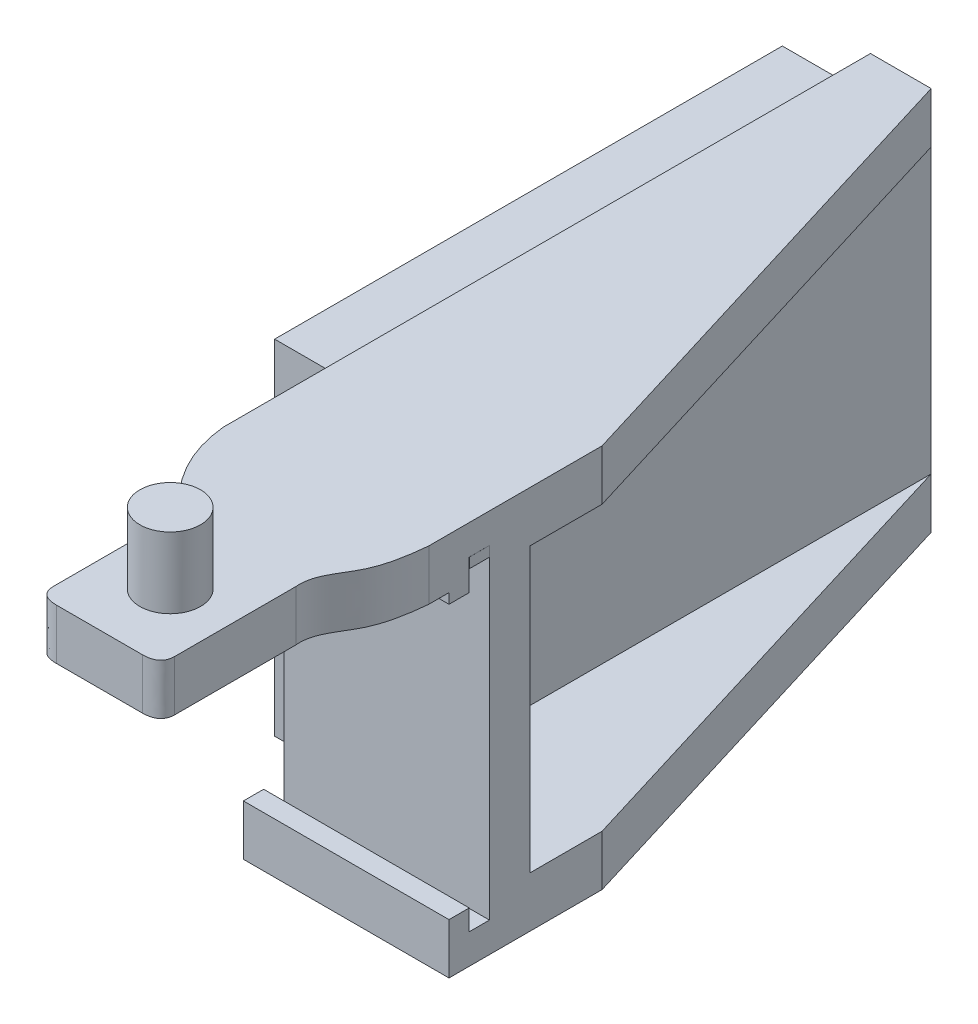
SolidWorks part; units mm, degrees
ref_plane "Alzado" through (0, 0, 0) normal (0, 0, 1) x (1, 0, 0)
ref_plane "Planta" through (0, 0, 0) normal (0, 1, 0) x (1, 0, 0)
ref_plane "Vista lateral" through (0, 0, 0) normal (1, 0, 0) x (0, 0, -1)
sketch "Croquis1" plane through (0, 0, 0) normal (0, 1, 0) x (1, 0, 0)
  line L0 (0, 30) -> (0, 0)
  line L1 (0, 0) -> (0, -2)
  line L2 (2.6172, -13.0183) -> (2.6172, -7.3446)
  line L4 (8.6172, -13.0183) -> (8.6172, -7.0183)
  line L5 (10.1631, 6.5705) -> (10.1631, 0)
  line L6 (10.1631, -2) -> (10.1631, 0)
  line L7 (10.1631, 6.5705) -> (3, 30)
  line L8 (3, 30) -> (0, 30)
  line L9 (3.4899, -13.7374) -> (7.7445, -13.7374)
  spline S0 degree 3 poles (8.6172, -7.0183) (8.5294, -6.0662) (9.8153, -4.7072) (10.0769, -2.8869) (10.1631, -2) knots 0 0 0 0 0.490317 1 1 1 1
  spline S1 degree 2 poles (0, -2) (0.2441, -4.453) (2.0609, -6.2319) knots 0 0 0 1 1 1
  spline S2 degree 2 poles (2.0609, -6.2319) (2.507, -6.7126) (2.6172, -7.3446) knots 0 0 0 1 1 1
  spline S3 degree 2 poles (2.6172, -13.0183) (2.6309, -13.735) (3.4899, -13.7374) knots 0 0 0 1 1 1
  spline S4 degree 2 poles (8.6172, -13.0183) (8.6035, -13.735) (7.7445, -13.7374) knots 0 0 0 1 1 1
  dimension "D1" = 3
  dimension "D2" = 30
  dimension "D3" = 24.5
  dimension "D4" = 6
  dimension "D6" = 2
  dimension "D7" = 6
extrude "Saliente-Extruir1" add sketch "Croquis1" along normal blind 19
sketch "Croquis2" plane through (0, 0, -30) normal (0, 0, -1) x (-1, 0, 0)
  line L0 (-3, 19) -> (-3, 16.5)
  line L1 (-3, 19) -> (-3, 0) construction
  line L2 (-3, 16.5) -> (-12.8726, 16.5)
  line L3 (-12.8726, 16.5) -> (-12.8726, 2.5)
  line L4 (-12.8726, 2.5) -> (-3, 2.5)
  line L5 (-3, 2.5) -> (-3, 16.5)
  line M6 (-3, 19) -> (-3, 0)
  dimension "D1" = 2.5
  dimension "D2" = 2.5
extrude "Cortar-Extruir1" cut sketch "Croquis2" against normal blind 27 contours L3 L4 L2 M6
sketch "Croquis10" plane through (0, 0, 0) normal (1, 0, 0) x (0, 0, -1)
  line L0 (1, 2.5) -> (1, 16.5)
  line L1 (1, 2.5) -> (-1, 2.5)
  line L2 (1, 16.5) -> (-13.7374, 16.5)
  line L3 (-13.7374, 19) -> (-13.7374, 0) construction
  line L4 (-13.7374, 16.5) -> (-13.7374, 0)
  line L5 (-1, 2.5) -> (-1, 0)
  line L7 (-2, 0) -> (6.5705, 0) construction
  line L8 (-1, 0) -> (-13.7374, 0)
  dimension "D1" = 2
extrude "Cortar-Extruir2" cut sketch "Croquis10" along normal through all both and the other way through all
sketch "Croquis11" plane through (0, 0, 0) normal (1, 0, 0) x (0, 0, -1)
  line L0 (1, 2.5) -> (1, 1.4799)
  line L1 (1, 1.4799) -> (0, 1.4799)
  line L2 (0, 1.4799) -> (0, 2.5)
  line L3 (-1, 2.5) -> (1, 2.5) construction
  line L4 (0, 2.5) -> (1, 2.5)
  line L5 (1, 16.5) -> (1, 17.5201)
  line L8 (1, 17.5201) -> (0, 17.5201)
  line L9 (0, 17.5201) -> (0, 16.5)
  line L10 (0, 16.5) -> (1, 16.5)
extrude "Cortar-Extruir3" cut sketch "Croquis11" along normal blind 33
sketch "Croquis12" plane through (0, 19, 0) normal (0, 1, 0) x (1, 0, 0)
  circle A0 centre (5.6172, -10.2374) radius 1.5
  dimension "D1" = 3
extrude "Saliente-Extruir3" add sketch "Croquis12" along normal blind 3.5
sketch "Croquis13" plane through (0, 0, 0) normal (-1, 0, 0) x (0, 0, 1)
  line L0 (-29.1429, 18) -> (-4.0429, 18)
  line L1 (-4.0429, 18) -> (-4.0429, 1)
  line L2 (-4.0429, 1) -> (-29.1429, 1)
  line L4 (-30, 19) -> (2, 19) construction
  line L5 (-29.1429, 1) -> (-29.1429, 18)
  line L6 (-30, 0) -> (1, 0) construction
  dimension "D1" = 1
  dimension "D2" = 1
  dimension "D3" = 25.1
extrude "Saliente-Extruir5" add sketch "Croquis13" along normal blind 3.5
sketch "Croquis16" plane through (10.1631, 0, 0) normal (1, 0, 0) x (0, 0, -1)
  line L0 (0, 16.5) -> (-1, 16.5)
  line L1 (0, 16.5) -> (-2, 16.5) construction
  line L2 (-1, 16.5) -> (-1, 16)
  line L3 (-1, 16) -> (0, 16)
  line L4 (0, 16) -> (0, 16.5)
  dimension "D1" = 0.5
extrude "Saliente-Extruir8" add sketch "Croquis16" against normal blind 10.162
sketch "Croquis19" plane through (0, 0, 0) normal (-1, 0, 0) x (0, 0, 1)
  line L0 (-1, 17.5201) -> (-1, 17.0201)
  line L1 (-1, 17.5201) -> (-1, 1.4799) construction
  line L2 (-1, 17.0201) -> (0, 17.0201)
  line L3 (0, 17.5201) -> (0, 16.5) construction
  line L4 (0, 17.0201) -> (0, 17.5201)
  line L5 (0, 17.5201) -> (-1, 17.5201)
  dimension "D1" = 0.5
extrude "Saliente-Extruir9" add sketch "Croquis19" against normal blind 10.165
